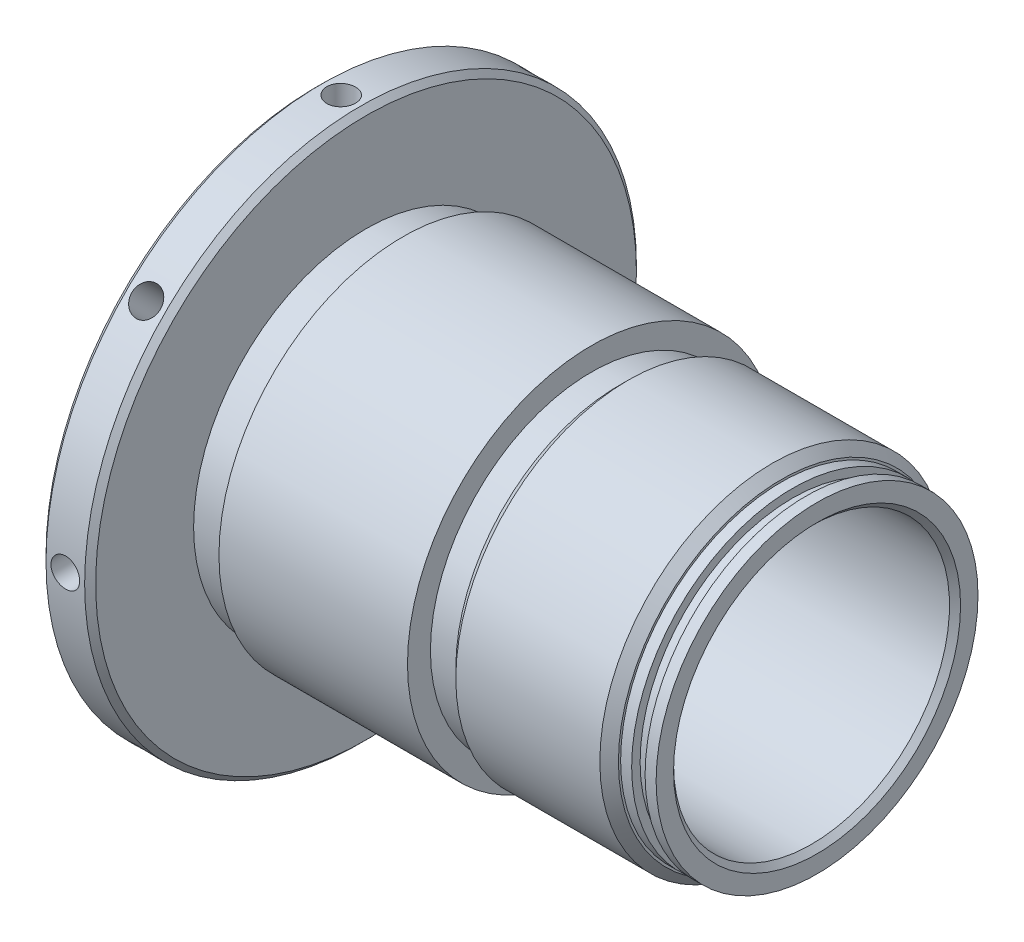
SolidWorks part; units mm, degrees
material "AISI 440C PER AMS 5630"
ref_plane "XY" through (0, 0, 0) normal (0, 0, 1) x (1, 0, 0)
ref_plane "XZ" through (0, 0, 0) normal (0, 1, 0) x (1, 0, 0)
ref_plane "YZ" through (0, 0, 0) normal (1, 0, 0) x (0, 0, -1)
sketch "Sketch1" plane through (0, 0, 0) normal (0, 0, 1) x (1, 0, 0)
  line L0 (0, 0) -> (105.4936, 0) construction
  line L1 (0, 19.558) -> (0, 25.3937)
  line L3 (19.304, 20.32) -> (19.304, 14.2311) construction
  line L4 (0, 25.3937) -> (62.2808, 25.3937)
  line L5 (17.78, 20.32) -> (20.828, 20.32)
  line L6 (62.2808, 19.0563) -> (22.0917, 19.0563)
  line L8 (17.018, 19.558) -> (0, 19.558)
  line L9 (20.828, 20.32) -> (22.0917, 19.0563)
  line L10 (17.78, 20.32) -> (17.018, 19.558)
  line L12 (62.2808, 25.3937) -> (62.2808, 19.0563)
  point P8 (25.908, 19.0563)
  point P18 (12.7, 19.558)
  dimension "D2" = 3.048
  dimension "D8" = 135
  dimension "D12" = 6.604
  dimension "D5" = 0.762
  dimension "D1" = 38.1127
  dimension "D3" = 39.116
  dimension "D4" = 19.304
  dimension "D6" = 62.2808
  dimension "D7" = 50.7873
  dimension "D11" = 13.208
  dimension "D13" = 135
revolve "Revolve1" add sketch "Sketch1" angle 360 about L0
sketch "Sketch2" plane through (0, 0, 0) normal (0, 0, 1) x (1, 0, 0)
  line L0 (62.2808, 25.3937) -> (0, 25.3937) construction
  line L1 (31.115, 25.3937) -> (62.2808, 25.3937)
  line L2 (31.115, 25.3937) -> (31.115, 22.225)
  line L3 (34.925, 23.8125) -> (57.3786, 23.8125)
  line L4 (62.2808, 25.3937) -> (62.2808, 22.225)
  line L5 (62.2808, -25.3937) -> (62.2808, 25.3937) construction
  line L6 (0, 0) -> (36.2503, 0) construction
  line L7 (2.8458, 22.5298) -> (34.9432, 22.5298) construction
  line L8 (34.925, 22.225) -> (34.925, 23.8125)
  line L9 (31.115, 22.225) -> (34.925, 22.225)
  line L10 (60.7568, 22.225) -> (62.2808, 22.225)
  line L12 (58.9026, 22.225) -> (58.9026, 21.0566)
  line L13 (58.9026, 21.0566) -> (60.7568, 21.0566)
  line L14 (60.7568, 22.225) -> (60.7568, 21.0566)
  line L16 (57.3786, 23.8125) -> (57.3786, 22.225)
  line L17 (57.3786, 22.225) -> (58.9026, 22.225)
  dimension "D3" = 44.45
  dimension "D1" = 5.207
  dimension "D2" = 47.625
  dimension "D4" = 45.0596
  dimension "D5" = 3.81
  dimension "D6" = 42.1132
  dimension "D7" = 1.524
  dimension "D8" = 1.8542
  dimension "D9" = 1.524
revolve "Cut-Revolve1" cut sketch "Sketch2" angle 360 about L6
cosmetic thread "Cosmetic Thread1" parameters "D2"=45.0596
ref_plane "Plane1" through (25.908, 0, 0) normal (1, 0, 0) x (0, 0, -1)
chamfer "Chamfer1" distance 0.762 angle 45 1 edges at (62.2808, 0, 19.0563)
sketch "Sketch3" plane through (0, 0, 0) normal (0, 0, 1) x (1, 0, 0)
  line L0 (0, 0) -> (-41.4207, 0) construction
  line L1 (17.018, 19.558) -> (0, 19.558) construction
  line L2 (0, 19.558) -> (-6.858, 19.558)
  line L3 (0, 19.558) -> (0, 38.1)
  line L4 (0, 38.1) -> (-6.858, 38.1)
  line L5 (-6.858, 19.558) -> (-6.858, 38.1)
  line L6 (0, 25.3937) -> (0, -25.3937) construction
  dimension "D1" = 6.858
  dimension "D2" = 76.2
revolve "Revolve2" add sketch "Sketch3" angle 360 about L0
sketch "Sketch5" plane through (0, 0, 0) normal (0, 0, 1) x (1, 0, 0)
  line L0 (31.115, 25.3937) -> (0, 25.3937) construction
  line L1 (5.08, 25.3937) -> (0, 25.3937)
  line L2 (5.08, 25.3937) -> (5.08, 23.8125)
  line L3 (5.08, 23.8125) -> (0, 23.8125)
  line L4 (0, 25.3937) -> (0, 23.8125)
  line L5 (0, -38.1) -> (0, 38.1) construction
  line L6 (23.3533, 0) -> (53.789, 0) construction
  line L7 (0, 0) -> (105.4936, 0) construction
  dimension "D1" = 5.08
  dimension "D2" = 47.625
revolve "Cut-Revolve2" cut sketch "Sketch5" angle 360 about L6
chamfer "Chamfer3" distance 0.762 angle 45 2 edges at (0, 0, -38.1) (-6.858, 0, -38.1)
ref_plane "Plane2" through (-3.429, 38.1, 0) normal (0, 1, 0) x (0, 0, 1)
sketch "Sketch6" plane through (-3.429, 38.1, 0) normal (0, 1, 0) x (0, 0, 1)
  line L0 (0, 0) -> (12.4962, 0) construction
  line L1 (37.338, 3.429) -> (-37.338, 3.429) construction
  line L2 (-19.558, -3.429) -> (19.558, -3.429) construction
  line L3 (0, 3.429) -> (0, 108.9226) construction
  circle A0 centre (0, 0) radius 1.9812
  dimension "D1" = 3.9624
extrude "Cut-Extrude2" cut sketch "Sketch6" against normal blind 6.35
chamfer "Chamfer4" distance 1.2827 angle 45 2 edges at (34.925, 0, 23.8125) (57.3786, 0, 23.8125)
pattern_circular "CirPattern2" count 8 every 45 about axis through (0, 0, 0) along (1, 0, 0) of "Cut-Extrude2"
sketch "Sketch7" plane through (-6.858, 0, 0) normal (-1, 0, 0) x (0, 0, 1)
  line L0 (-11.1071, 26.3063) -> (11.1071, 26.3063) construction
  line L1 (0, 26.3063) -> (0, 0) construction
  text T0 "STG 0-1"
extrude "Extrude1" cut sketch "Sketch7" against normal blind 0.0254
